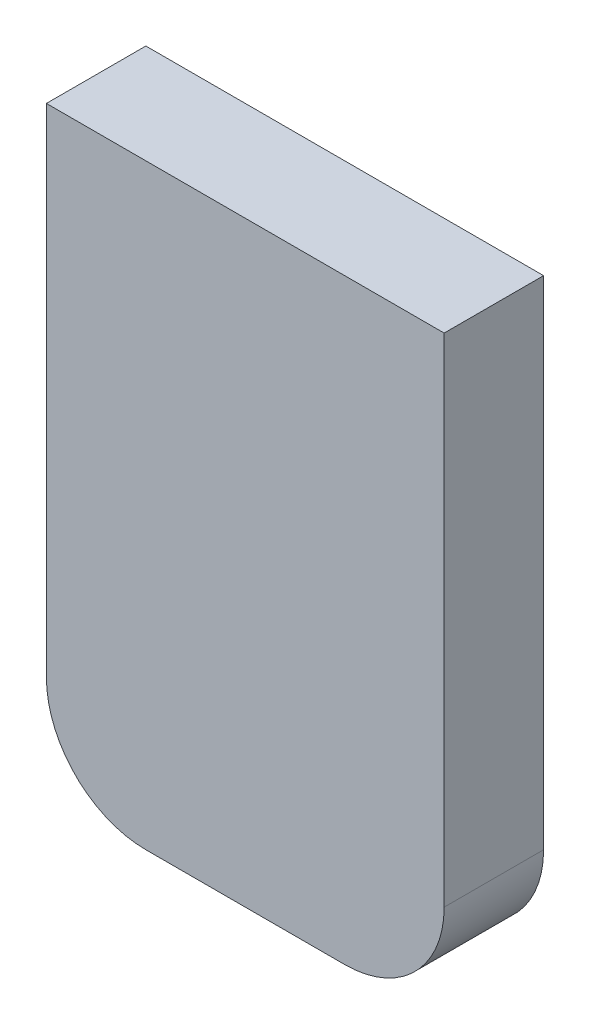
SolidWorks part; units mm, degrees
ref_plane "Alzado" through (0, 0, 0) normal (0, 0, 1) x (1, 0, 0)
ref_plane "Planta" through (0, 0, 0) normal (0, 1, 0) x (1, 0, 0)
ref_plane "Vista lateral" through (0, 0, 0) normal (1, 0, 0) x (0, 0, -1)
sketch "Croquis1" plane through (0, 0, 0) normal (0, 0, 1) x (1, 0, 0)
  line L1 (-80.6068, 54.1736) -> (-40.6068, 54.1736)
  line L2 (-90.6068, 44.1736) -> (-90.6068, 4.1736)
  line L3 (-80.6068, -5.8264) -> (-40.6068, -5.8264)
  line L4 (-30.6068, 44.1736) -> (-30.6068, 4.1736)
  line L5 (-90.6068, 54.1736) -> (-30.6068, -5.8264) construction
  line L6 (-90.6068, -5.8264) -> (-30.6068, 54.1736) construction
  arc A0 (-80.6068, 54.1736) -> (-90.6068, 44.1736) centre (-80.6068, 44.1736) ccw
  arc A1 (-30.6068, 44.1736) -> (-40.6068, 54.1736) centre (-40.6068, 44.1736) ccw
  arc A2 (-30.6068, 4.1736) -> (-40.6068, -5.8264) centre (-40.6068, 4.1736) cw
  arc A3 (-80.6068, -5.8264) -> (-90.6068, 4.1736) centre (-80.6068, 4.1736) cw
  point P0 (-60.6068, 24.1736)
  dimension "D3" = 10
  dimension "D4" = 10
  dimension "D5" = 10
  dimension "D1" = 60
  dimension "D2" = 60
extrude "Saliente-Extruir1" add sketch "Croquis1" along normal blind 50
sketch "Croquis2" plane through (0, -5.8264, 0) normal (0, -1, 0) x (1, 0, 0)
  line L0 (-30.6068, 0) -> (-70.6068, 0)
  line L1 (-70.6068, 0) -> (-70.6068, 50)
  line L2 (-80.6068, 50) -> (-40.6068, 50) construction
  line L3 (-70.6068, 50) -> (-30.6068, 50)
  line L4 (-30.6068, 50) -> (-30.6068, 0) construction
  line L5 (-30.6068, 50) -> (-30.6068, 0)
  dimension "D1" = 40
extrude "Saliente-Extruir2" add sketch "Croquis2" along normal blind 60 and the other way blind 31
fillet "Redondeo1" radius 10 1 edges at (-30.6068, -65.8264, 25)
fillet "Redondeo2" radius 10 1 edges at (-70.6068, -65.8264, 25)
sketch "Croquis3" plane through (-30.6068, 0, 0) normal (1, 0, 0) x (0, 0, -1)
  line L1 (-50, -65.8264) -> (0, -65.8264) construction
  line L2 (-40, -65.8264) -> (-40, -5.8264)
  line L3 (0, -5.8264) -> (-50, -5.8264) construction
  line L4 (-40, -5.8264) -> (-50, -5.8264)
  line L6 (-50, -5.8264) -> (-90.9544, -5.8264)
  line L7 (-90.9544, -5.8264) -> (-90.9544, 59.7553)
  line L8 (-90.9544, 59.7553) -> (17.5778, 59.7553)
  line L9 (17.5778, 59.7553) -> (17.5778, -73.5983)
  line L10 (17.5778, -73.5983) -> (-40, -73.5983)
  line L11 (-40, -73.5983) -> (-40, -65.8264)
extrude "Cortar-Extruir1" cut sketch "Croquis3" against normal blind 74
shell "Vaciado1" thickness 3
sketch "Croquis4" plane through (0, 0, 47) normal (0, 0, -1) x (-1, 0, 0)
  line L0 (50.6068, -8.8264) -> (50.6068, -62.8264) construction
  line L1 (67.6068, -8.8264) -> (33.6068, -8.8264) construction
  line L2 (40.6068, -62.8264) -> (60.6068, -62.8264) construction
  line L3 (33.6068, -35.8264) -> (67.6068, -35.8264) construction
  line L4 (33.6068, -8.8264) -> (33.6068, -55.8264) construction
  line L5 (67.6068, -8.8264) -> (67.6068, -55.8264) construction
  line L6 (60.6068, -65.8264) -> (40.6068, -65.8264) construction
  line L7 (40.4068, -61.0264) -> (60.8068, -61.0264)
  line L8 (40.4068, -61.0264) -> (40.4068, -11.0264)
  line L9 (40.4068, -11.0264) -> (60.8068, -11.0264)
  line L10 (60.8068, -61.0264) -> (60.8068, -11.0264)
  line L11 (40.4068, -61.0264) -> (60.8068, -11.0264) construction
  line L12 (40.4068, -11.0264) -> (60.8068, -61.0264) construction
  line L13 (70.6068, -55.8264) -> (70.6068, -5.8264) construction
  line L14 (63.8068, -64.0264) -> (63.8068, -8.0264)
  line L15 (37.4068, -8.0264) -> (63.8068, -8.0264)
  line L16 (37.4068, -64.0264) -> (37.4068, -8.0264)
  line L17 (37.4068, -64.0264) -> (63.8068, -64.0264)
  point P12 (50.6068, -36.0264)
  dimension "D1" = 4.8
  dimension "D2" = 9.8
  dimension "D3" = 50
  dimension "D4" = 3
extrude "Saliente-Extruir3" add sketch "Croquis4" along normal up to surface (7 mm away) up to face at (-50.6068, -42.9764, 40)
